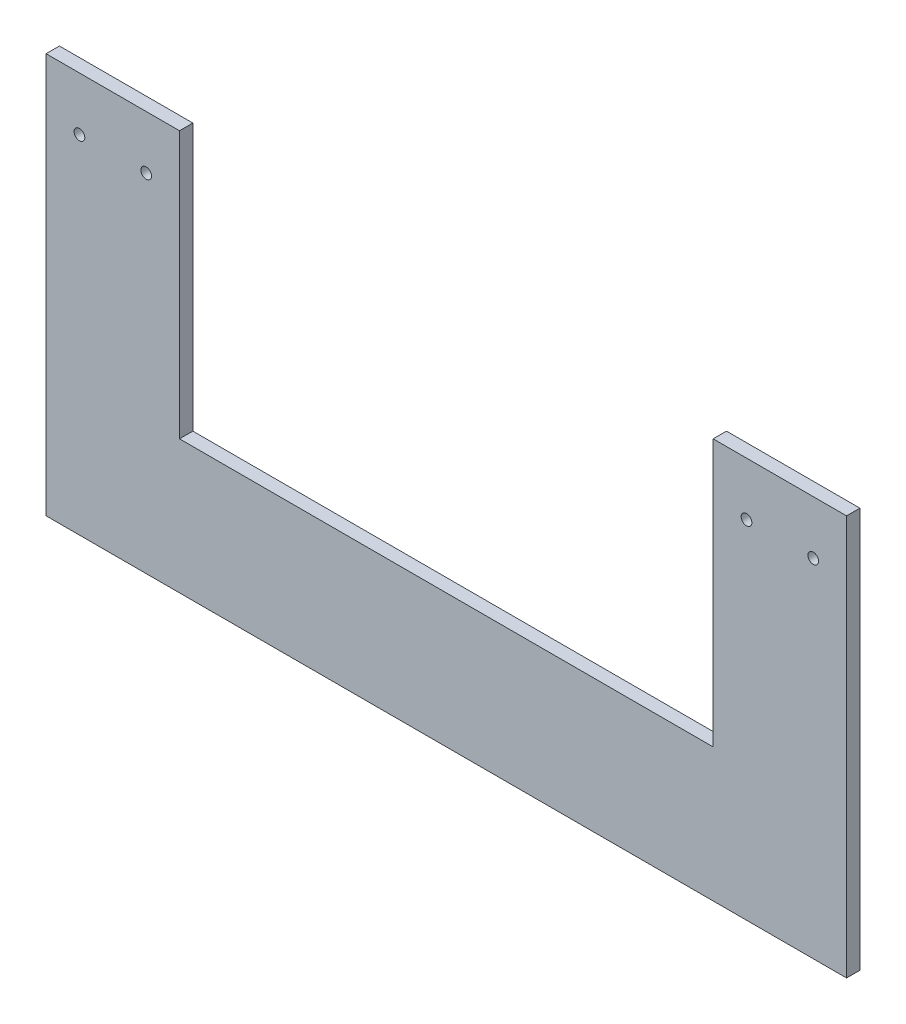
SolidWorks part; units mm, degrees
ref_plane "Front Plane" through (0, 0, 0) normal (0, 0, 1) x (1, 0, 0)
ref_plane "Top Plane" through (0, 0, 0) normal (0, 1, 0) x (1, 0, 0)
ref_plane "Right Plane" through (0, 0, 0) normal (1, 0, 0) x (0, 0, -1)
sketch "Sketch2" plane through (0, 0, 0) normal (0, 0, 1) x (1, 0, 0)
  line L0 (-54.7127, 76.2496) -> (-29.7127, 76.2496) construction
  line L1 (-54.7127, 96.2496) -> (-4.7127, 96.2496)
  line L2 (-54.7127, 96.2496) -> (-54.7127, -53.7504)
  line L3 (-54.7127, -53.7504) -> (245.2873, -53.7504)
  line L4 (245.2873, 96.2496) -> (245.2873, -53.7504)
  line L5 (195.2873, 96.2496) -> (195.2873, -3.7504)
  line L6 (-4.7127, -3.7504) -> (195.2873, -3.7504)
  line L7 (-4.7127, 96.2496) -> (-4.7127, -3.7504)
  line L8 (-4.7127, 46.2496) -> (-4.7127, -3.7504) construction
  line L9 (195.2873, 46.2496) -> (195.2873, -3.7504) construction
  line L10 (195.2873, 96.2496) -> (245.2873, 96.2496)
  line L11 (-54.7127, 96.2496) -> (245.2873, 96.2496) construction
  line L12 (-4.7127, 46.2496) -> (195.2873, 46.2496) construction
  line L13 (220.2873, 76.2496) -> (245.2873, 76.2496) construction
  line L14 (-29.7127, 96.2496) -> (-29.7127, 76.2496) construction
  line L15 (220.2873, 76.2496) -> (220.2873, 96.2496) construction
  circle A0 centre (-42.2127, 76.2496) radius 2
  circle A1 centre (232.7873, 76.2496) radius 2
  circle A2 centre (207.7873, 76.2496) radius 2
  circle A3 centre (-17.2127, 76.2496) radius 2
  dimension "D5" = 4
  dimension "D6" = 4
  dimension "D1" = 300
  dimension "D2" = 150
  dimension "D4" = 20
  dimension "D3" = 50
extrude "Boss-Extrude1" add sketch "Sketch2" along normal blind 5
